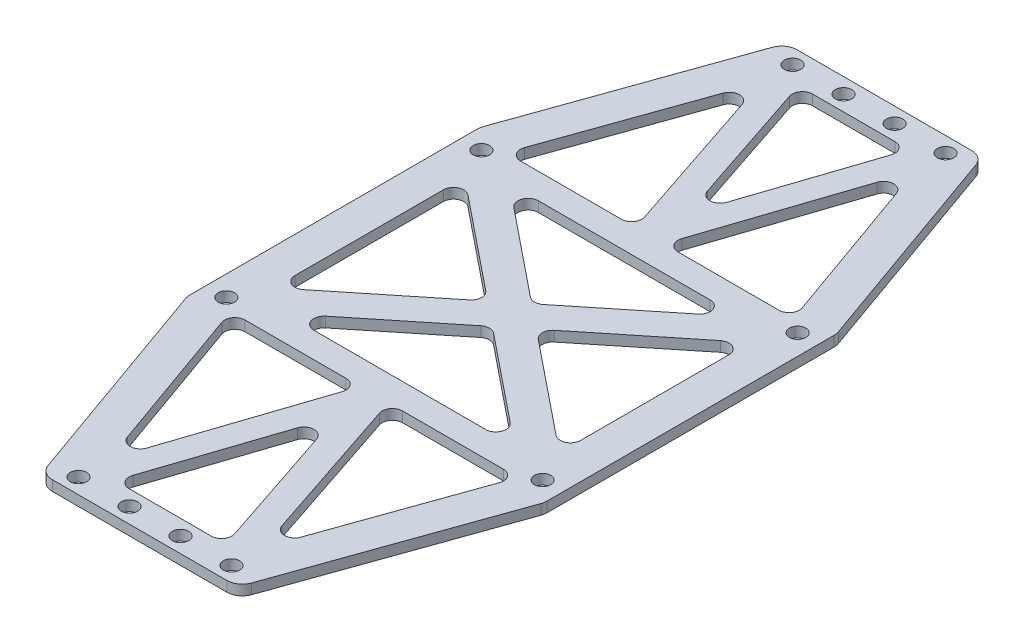
SolidWorks part; units mm, degrees
material "Hexcel AS4C (3000 丝)"
ref_plane "前视基准面" through (0, 0, 0) normal (0, 0, 1) x (1, 0, 0)
ref_plane "上视基准面" through (0, 0, 0) normal (0, 1, 0) x (1, 0, 0)
ref_plane "右视基准面" through (0, 0, 0) normal (1, 0, 0) x (0, 0, -1)
sketch "草图1" plane through (0, 0, 0) normal (0, 1, 0) x (1, 0, 0)
  line L0 (-15, 70) -> (-5, 70) construction
  line L1 (31, 25) -> (-31, 25) construction
  line L2 (31, 25) -> (31, -25) construction
  line L3 (31, -25) -> (-31, -25) construction
  line L4 (-31, 25) -> (-31, -25) construction
  line L5 (31, 25) -> (-31, -25) construction
  line L6 (31, -25) -> (-31, 25) construction
  line L7 (15, -70) -> (-15, -70) construction
  line L8 (15, -70) -> (15, 70) construction
  line L9 (15, 70) -> (-15, 70) construction
  line L10 (-15, -70) -> (-15, 70) construction
  line L11 (15, -70) -> (-15, 70) construction
  line L12 (15, 70) -> (-15, -70) construction
  line L13 (-15, 70) -> (-15, -70) construction
  line L14 (0, 0) -> (0, 70) construction
  line L15 (35, -28.6749) -> (19.24, -73)
  line L16 (-19.24, 73) -> (-35, 28.6749)
  line L17 (-35, 28.6749) -> (-35, -28.6749)
  line L18 (-35, -28.6749) -> (-19.24, -73)
  line L19 (35, 28.6749) -> (35, -28.6749)
  line L20 (19.24, 73) -> (35, 28.6749)
  line L21 (-19.24, 73) -> (19.24, 73)
  line L22 (-19.24, -73) -> (19.24, -73)
  line L23 (-15, 70) -> (-31, 25) construction
  line L24 (-31, -25) -> (-15, -70) construction
  circle A0 centre (-31, 25) radius 1.6
  circle A1 centre (-31, -25) radius 1.6
  circle A2 centre (31, -25) radius 1.6
  circle A3 centre (31, 25) radius 1.6
  circle A4 centre (-15, 70) radius 1.6
  circle A5 centre (-5, 70) radius 1.6
  circle A6 centre (5, 70) radius 1.6
  circle A7 centre (15, 70) radius 1.6
  circle A8 centre (-5, -70) radius 1.6
  circle A9 centre (5, -70) radius 1.6
  circle A10 centre (15, -70) radius 1.6
  circle A11 centre (-15, -70) radius 1.6
  point P0 (0, 0)
  point P10 (0, 0)
  dimension "D3" = 3.2
  dimension "D4" = 3.2
  dimension "D1" = 62
  dimension "D2" = 50
  dimension "D7" = 10
  dimension "D8" = 140
  dimension "D9" = 3
  dimension "D10" = 3
  dimension "D11" = 5
  dimension "D12" = 5
  dimension "D13" = 4
  dimension "D5" = 4
  dimension "D6" = 2
extrude "凸台-拉伸1" add sketch "草图1" along normal blind 2
sketch "草图2" plane through (0, 2, 0) normal (0, 1, 0) x (1, 0, 0)
  line L0 (-31, 25) -> (-31, -25) construction
  line L1 (-31, -25) -> (0, 0) construction
  line L2 (0, 0) -> (31, 25) construction
  line L3 (31, 25) -> (31, -25) construction
  line L4 (31, -25) -> (0, 0) construction
  line L5 (-31, 25) -> (31, 25) construction
  line L6 (-31, 25) -> (0, 0) construction
  line L7 (-31, -25) -> (0, -25) construction
  line L8 (-31, -25) -> (-15, -70) construction
  line L9 (-15, -70) -> (15, -70) construction
  line L10 (15, -70) -> (31, -25) construction
  line L11 (15, -70) -> (0, -25) construction
  line L12 (0, -25) -> (-15, -70) construction
  line L13 (0, 0) -> (31, 0) construction
  line L14 (0, -25) -> (31, -25) construction
  line L15 (-3.6523, -29.6325) -> (-13.2246, -58.3494)
  line L16 (-27.2169, -29.67) -> (-17.0064, -58.3869)
  line L17 (-25.3325, -27) -> (-5.5497, -27)
  line L18 (-1.8974, -40.1789) -> (-9.9602, -64.3675)
  line L19 (-8.0629, -67) -> (8.0629, -67)
  line L20 (9.9602, -64.3675) -> (1.8974, -40.1789)
  line L21 (5.5497, -27) -> (25.3325, -27)
  line L22 (17.0064, -58.3869) -> (27.2169, -29.67)
  line L23 (13.2246, -58.3494) -> (3.6523, -29.6325)
  line L24 (-28, 14.5444) -> (-28, -14.5444)
  line L25 (-24.7445, -16.1012) -> (-6.7094, -1.5568)
  line L26 (-24.7445, 16.1012) -> (-6.7094, 1.5568)
  line L27 (24.7445, -16.1012) -> (6.7094, -1.5568)
  line L28 (6.7094, 1.5568) -> (24.7445, 16.1012)
  line L29 (28, 14.5444) -> (28, -14.5444)
  line L30 (-18.0906, -18.4432) -> (-1.2555, -4.8665)
  line L31 (18.0906, -18.4432) -> (1.2555, -4.8665)
  line L32 (0, -22) -> (16.8351, -22)
  line L33 (-16.8351, -22) -> (0, -22)
  line L34 (-2.7749, -27) -> (-15.061, -63.8585) construction
  line L35 (-28.1662, -27) -> (-2.7749, -27) construction
  line L36 (-28.1662, -27) -> (-15.061, -63.8585) construction
  line L37 (10.8377, -67) -> (0, -34.4868) construction
  line L38 (-10.8377, -67) -> (10.8377, -67) construction
  line L39 (0, -34.4868) -> (-10.8377, -67) construction
  line L40 (2.7749, -27) -> (28.1662, -27) construction
  line L41 (15.061, -63.8585) -> (28.1662, -27) construction
  line L42 (15.061, -63.8585) -> (2.7749, -27) construction
  line L43 (28, -18.7267) -> (4.779, 0) construction
  line L44 (28, 18.7267) -> (28, -18.7267) construction
  line L45 (4.779, 0) -> (28, 18.7267) construction
  line L46 (0, -22) -> (22.501, -22) construction
  line L47 (22.501, -22) -> (0, -3.854) construction
  line L48 (-22.501, -22) -> (0, -3.854) construction
  line L49 (-22.501, -22) -> (0, -22) construction
  line L50 (-28, -18.7267) -> (-4.779, 0) construction
  line L51 (-28, 18.7267) -> (-28, -18.7267) construction
  line L52 (-28, 18.7267) -> (-4.779, 0) construction
  line L53 (-16.8351, 22) -> (0, 22)
  line L54 (0, 22) -> (16.8351, 22)
  line L55 (18.0906, 18.4432) -> (1.2555, 4.8665)
  line L56 (-18.0906, 18.4432) -> (-1.2555, 4.8665)
  line L57 (9.9602, 64.3675) -> (1.8974, 40.1789)
  line L58 (-8.0629, 67) -> (8.0629, 67)
  line L59 (-1.8974, 40.1789) -> (-9.9602, 64.3675)
  line L60 (13.2246, 58.3494) -> (3.6523, 29.6325)
  line L61 (17.0064, 58.3869) -> (27.2169, 29.67)
  line L62 (5.5497, 27) -> (25.3325, 27)
  line L63 (-25.3325, 27) -> (-5.5497, 27)
  line L64 (-27.2169, 29.67) -> (-17.0064, 58.3869)
  line L65 (-3.6523, 29.6325) -> (-13.2246, 58.3494)
  arc A0 (-3.6523, -29.6325) -> (-5.5497, -27) centre (-5.5497, -29) ccw
  arc A1 (-27.2169, -29.67) -> (-25.3325, -27) centre (-25.3325, -29) cw
  arc A2 (-13.2246, -58.3494) -> (-17.0064, -58.3869) centre (-15.122, -57.7169) cw
  arc A3 (9.9602, -64.3675) -> (8.0629, -67) centre (8.0629, -65) cw
  arc A4 (-8.0629, -67) -> (-9.9602, -64.3675) centre (-8.0629, -65) cw
  arc A5 (-1.8974, -40.1789) -> (1.8974, -40.1789) centre (0, -40.8114) cw
  arc A6 (25.3325, -27) -> (27.2169, -29.67) centre (25.3325, -29) cw
  arc A7 (17.0064, -58.3869) -> (13.2246, -58.3494) centre (15.122, -57.7169) cw
  arc A8 (3.6523, -29.6325) -> (5.5497, -27) centre (5.5497, -29) cw
  arc A9 (24.7445, -16.1012) -> (28, -14.5444) centre (26, -14.5444) ccw
  arc A10 (28, 14.5444) -> (24.7445, 16.1012) centre (26, 14.5444) ccw
  arc A11 (6.7094, -1.5568) -> (6.7094, 1.5568) centre (7.9649, 0) cw
  arc A12 (16.8351, -22) -> (18.0906, -18.4432) centre (16.8351, -20) ccw
  arc A13 (1.2555, -4.8665) -> (-1.2555, -4.8665) centre (0, -6.4233) ccw
  arc A14 (-16.8351, -22) -> (-18.0906, -18.4432) centre (-16.8351, -20) cw
  arc A15 (-24.7445, -16.1012) -> (-28, -14.5444) centre (-26, -14.5444) cw
  arc A16 (-6.7094, -1.5568) -> (-6.7094, 1.5568) centre (-7.9649, 0) ccw
  arc A17 (-24.7445, 16.1012) -> (-28, 14.5444) centre (-26, 14.5444) ccw
  arc A18 (16.8351, 22) -> (18.0906, 18.4432) centre (16.8351, 20) cw
  arc A19 (1.2555, 4.8665) -> (-1.2555, 4.8665) centre (0, 6.4233) cw
  arc A20 (-16.8351, 22) -> (-18.0906, 18.4432) centre (-16.8351, 20) ccw
  arc A21 (9.9602, 64.3675) -> (8.0629, 67) centre (8.0629, 65) ccw
  arc A22 (-8.0629, 67) -> (-9.9602, 64.3675) centre (-8.0629, 65) ccw
  arc A23 (-1.8974, 40.1789) -> (1.8974, 40.1789) centre (0, 40.8114) ccw
  arc A24 (17.0064, 58.3869) -> (13.2246, 58.3494) centre (15.122, 57.7169) ccw
  arc A25 (25.3325, 27) -> (27.2169, 29.67) centre (25.3325, 29) ccw
  arc A26 (3.6523, 29.6325) -> (5.5497, 27) centre (5.5497, 29) ccw
  arc A27 (-27.2169, 29.67) -> (-25.3325, 27) centre (-25.3325, 29) ccw
  arc A28 (-3.6523, 29.6325) -> (-5.5497, 27) centre (-5.5497, 29) cw
  arc A29 (-13.2246, 58.3494) -> (-17.0064, 58.3869) centre (-15.122, 57.7169) ccw
  dimension "D7" = 2
  dimension "D1" = 2
  dimension "D2" = 3
  dimension "D3" = 2
  dimension "D4" = 3
  dimension "D5" = 3
  dimension "D6" = 3
extrude "切除-拉伸1" cut sketch "草图2" against normal through all
fillet "圆角1" radius 3 8 edges at (-35, 1, 28.6749) (-35, 1, -28.6749) (-19.24, 1, -73) (19.24, 1, -73) (35, 1, -28.6749) (35, 1, 28.6749) (19.24, 1, 73) (-19.24, 1, 73)
